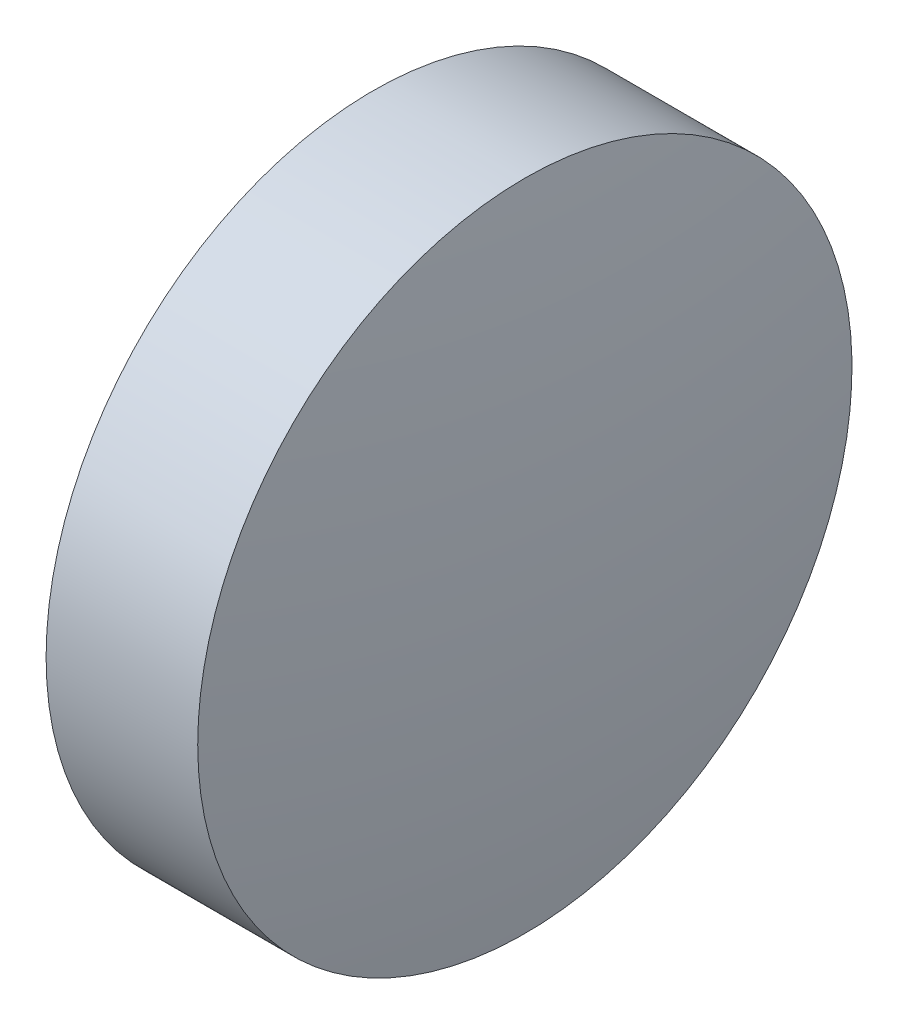
SolidWorks part; units mm, degrees
ref_plane "前视基准面" through (0, 0, 0) normal (0, 0, 1) x (1, 0, 0)
ref_plane "上视基准面" through (0, 0, 0) normal (0, 1, 0) x (1, 0, 0)
ref_plane "右视基准面" through (0, 0, 0) normal (1, 0, 0) x (0, 0, -1)
sketch "草图1" plane through (0, 0, 0) normal (0, 0, 1) x (1, 0, 0)
  line L0 (798.2663, 336.5592) -> (852.0493, 336.5592) construction
  line L1 (818.4629, 336.5592) -> (818.4629, 339.7092)
  line L2 (818.4629, 339.7092) -> (819.9229, 339.7092)
  line L3 (818.4629, 336.5592) -> (820.1629, 336.5592)
  arc A0 (820.1629, 336.5592) -> (819.9229, 339.7092) centre (799.371, 336.5592) ccw
revolve "旋转1" add sketch "草图1" angle 360 about L0
